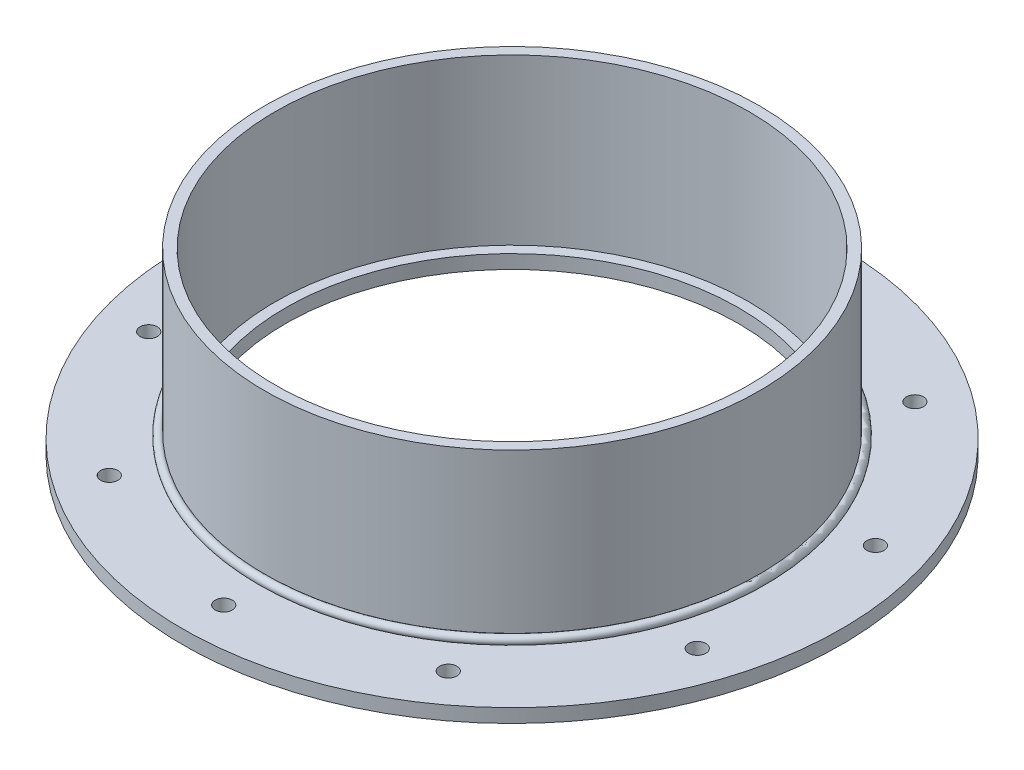
SolidWorks part; units mm, degrees
ref_plane "Front" through (0, 0, 0) normal (0, 0, 1) x (1, 0, 0)
ref_plane "Top" through (0, 0, 0) normal (0, 1, 0) x (1, 0, 0)
ref_plane "Right" through (0, 0, 0) normal (1, 0, 0) x (0, 0, -1)
sketch "Sketch1" plane through (0, 0, 0) normal (0, 0, 1) x (1, 0, 0)
  line L0 (0, 0) -> (0, 26.292) construction
  line L1 (-104.775, 0) -> (-152.4, 0)
  line L2 (-104.775, 0) -> (-104.775, 6.35)
  line L3 (-104.775, 6.35) -> (-152.4, 6.35)
  line L4 (-152.4, 0) -> (-152.4, 6.35)
  dimension "D1" = 6.35
  dimension "D2" = 304.8
  dimension "D3" = 209.55
revolve "Revolve1" add sketch "Sketch1" angle 360 about L0
sketch "Sketch2" plane through (0, 0, 0) normal (0, 0, 1) x (1, 0, 0)
  line L0 (152.4, 6.35) -> (-152.4, 6.35) construction
  line L1 (-114.3, 6.35) -> (-109.5375, 6.35)
  line L2 (-114.3, 6.35) -> (-114.3, 82.55)
  line L3 (-114.3, 82.55) -> (-109.5375, 82.55)
  line L4 (-109.5375, 6.35) -> (-109.5375, 82.55)
  line L5 (0, 0) -> (0, 56.4767) construction
  line L6 (-152.4, 0) -> (152.4, 0) construction
  dimension "D1" = 4.7625
  dimension "D2" = 219.075
  dimension "D3" = 82.55
revolve "Revolve2" add sketch "Sketch2" angle 360 about L5
sketch "Sketch3" plane through (0, 0, 0) normal (0, 0, 1) x (1, 0, 0)
  line L0 (-115.5234, 7.5734) -> (-114.3, 6.35) construction
  line L1 (152.4, 6.35) -> (-152.4, 6.35) construction
  line L2 (-114.3, 6.35) -> (-117.0858, 6.35)
  line L3 (-114.3, 82.55) -> (-114.3, 6.35) construction
  line L4 (-114.3, 9.1358) -> (-114.3, 6.35)
  line L5 (0, 0) -> (0, 19.0297) construction
  arc A0 (-114.3, 9.1358) -> (-117.0858, 6.35) centre (-115.5234, 7.5734) ccw
  dimension "D1" = 3.9688
  dimension "D2" = 45
  dimension "D3" = 2.7858
revolve "Revolve3" add sketch "Sketch3" angle 360 about L5
sketch "Sketch4" plane through (0, 6.35, 0) normal (0, 1, 0) x (1, 0, 0)
  circle A0 centre (0, 133.35) radius 3.9687
  circle A1 centre (0, 0) radius 133.35 construction
  dimension "D1" = 266.7
  dimension "D2" = 7.9375
extrude "Cut-Extrude1" cut sketch "Sketch4" against normal through all
pattern_circular "CirPattern1" count 10 over 360 about axis through (0, 0, 0) along (0, 1, 0) of "Cut-Extrude1"
